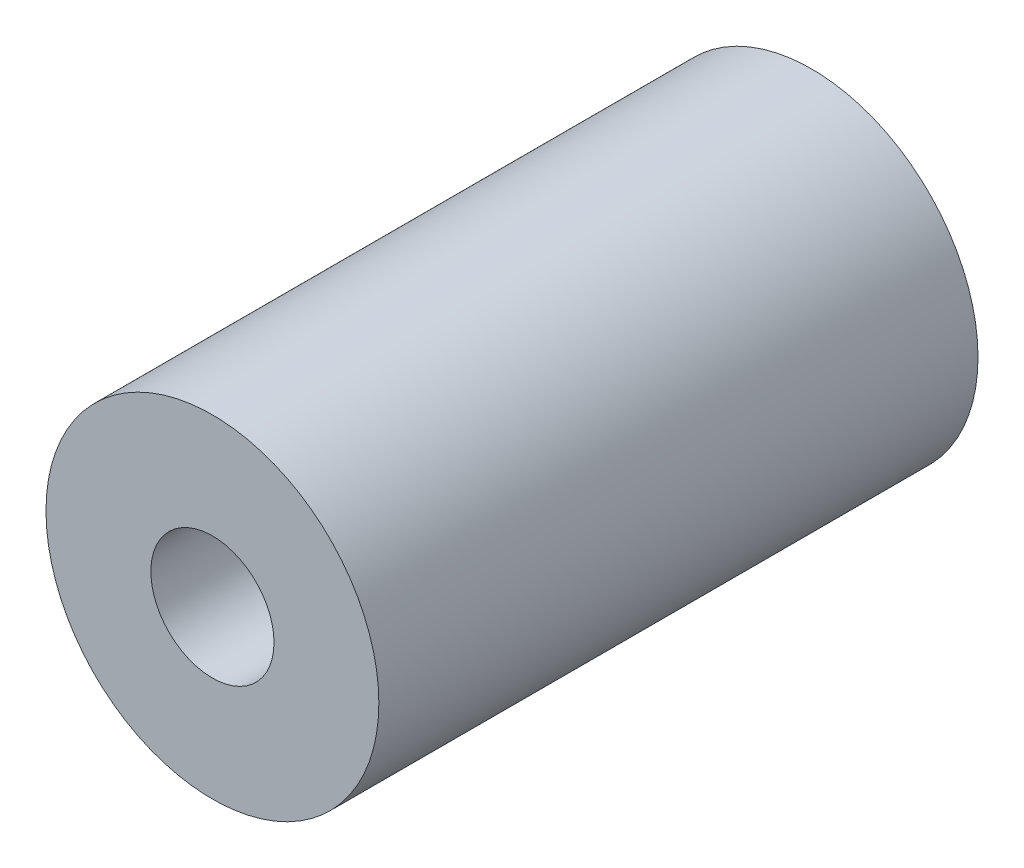
SolidWorks part; units mm, degrees
material "2024 Alloy"
ref_plane "Front Plane" through (0, 0, 0) normal (0, 0, 1) x (1, 0, 0)
ref_plane "Top Plane" through (0, 0, 0) normal (0, 1, 0) x (1, 0, 0)
ref_plane "Right Plane" through (0, 0, 0) normal (1, 0, 0) x (0, 0, -1)
sketch "Sketch1" plane through (0, 0, 0) normal (0, 0, 1) x (1, 0, 0)
  circle A0 centre (0, 0) radius 1.85
  circle A1 centre (0, 0) radius 5
  dimension "D1" = 3.7
  dimension "D2" = 10
extrude "Boss-Extrude1" add sketch "Sketch1" along normal blind 18
